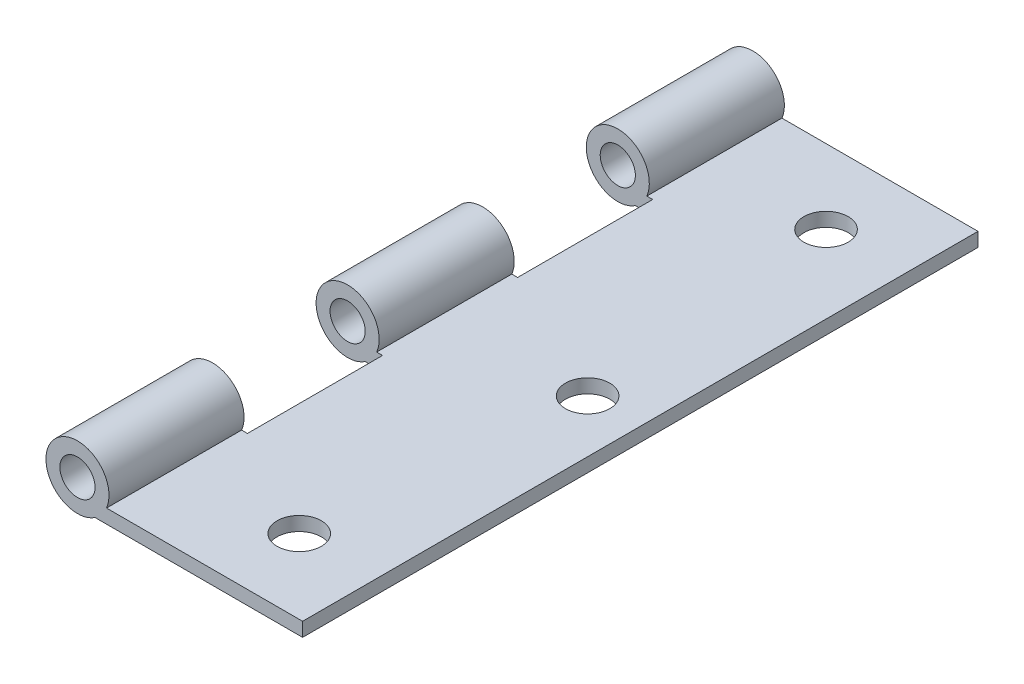
SolidWorks part; units mm, degrees
ref_plane "Front Plane" through (0, 0, 0) normal (0, 0, 1) x (1, 0, 0)
ref_plane "Top Plane" through (0, 0, 0) normal (0, 1, 0) x (1, 0, 0)
ref_plane "Right Plane" through (0, 0, 0) normal (1, 0, 0) x (0, 0, -1)
ref_plane "Plane1" through (0, 0, 38.1) normal (0, 0, 1) x (1, 0, 0)
sketch "Sketch1" plane through (0, 0, 38.1) normal (0, 0, 1) x (1, 0, 0)
  line L0 (25.4, -2.9508) -> (25.4, -1.376)
  line L1 (25.4, -1.376) -> (3.279, -1.376)
  line L2 (1.9844, -2.9508) -> (25.4, -2.9508)
  arc A0 (3.279, -1.376) -> (1.9844, -2.9508) centre (0, 0) ccw
extrude "Boss-Extrude1" add sketch "Sketch1" against normal blind 76.2
ref_plane "Plane2" through (0, 0, -22.86) normal (0, 0, -1) x (-1, 0, 0)
sketch "Sketch6" plane through (0, 0, -22.86) normal (0, 0, -1) x (-1, 0, 0)
  line L0 (-3.937, -1.376) -> (-3.937, -2.9508)
  line L1 (-3.937, -2.9508) -> (-1.9844, -2.9508)
  line L2 (-3.279, -1.376) -> (-3.937, -1.376)
  arc A0 (-1.9844, -2.9508) -> (-3.279, -1.376) centre (0, 0) ccw
extrude "Cut-Extrude1" cut sketch "Sketch6" against normal blind 15.24
ref_plane "Plane3" through (0, 0, 7.62) normal (0, 0, -1) x (-1, 0, 0)
sketch "Sketch12" plane through (0, 0, 7.62) normal (0, 0, -1) x (-1, 0, 0)
  line L0 (-3.937, -1.376) -> (-3.937, -2.9508)
  line L1 (-3.937, -2.9508) -> (-1.9844, -2.9508)
  line L2 (-3.279, -1.376) -> (-3.937, -1.376)
  arc A0 (-1.9844, -2.9508) -> (-3.279, -1.376) centre (0, 0) ccw
extrude "Cut-Extrude2" cut sketch "Sketch12" against normal blind 15.24
hole_wizard "CSK for M3 Flat Head Machine Screw1" positions "Sketch14" profile "Sketch13" countersink size "M3" standard "ANSI Metric"
sketch "Sketch14" plane through (0, -1.376, 0) normal (0, 1, 0) x (1, 0, 0)
  point P0 (16.637, 29.718)
  point P1 (16.637, -29.718)
  point P2 (19.4564, 0)
sketch "Sketch13" plane through (16.637, -1.376, -29.718) normal (1, 0, 0) x (0, 0, 1)
  line L0 (0, 0) -> (0, 2.18)
  line L1 (0, 2.18) -> (1.7526, 2.18)
  line L2 (1.7526, 2.18) -> (1.7526, 0.7874)
  line L3 (1.7526, 0.7874) -> (2.4371, 0)
  line L5 (2.4371, 0) -> (0, 0)
  line L6 (-1.7526, 0.7874) -> (-2.4371, 0) construction
  line L11 (0, -6.35) -> (0, 107.95) construction
  dimension "Thru Hole Dia." = 3.5052
  dimension "Thru Hole Depth" = 2.18
  dimension "Near C'Sink Dia." = 4.8742
  dimension "Near C'Sink Angle" = 82
hole_wizard "M3.5 Clearance Hole1" positions "Sketch16" profile "Sketch15" hole size "M3.5" standard "ANSI Metric"
sketch "Sketch16" plane through (0, 0, 38.1) normal (0, 0, 1) x (1, 0, 0)
  point P0 (0, 0)
sketch "Sketch15" plane through (0, 0, 38.1) normal (1, 0, 0) x (0, -1, 0)
  line L0 (0, 0) -> (0, 15.24)
  line L1 (0, 15.24) -> (1.9844, 15.24)
  line L2 (1.9844, 15.24) -> (1.9844, 0)
  line L5 (1.9844, 0) -> (0, 0)
  line L11 (0, -6.35) -> (0, 107.95) construction
  dimension "Thru Hole Dia." = 3.9688
  dimension "Thru Hole Depth" = 15.24
hole_wizard "M3.5 Clearance Hole2" positions "Sketch18" profile "Sketch17" hole size "M3.5" standard "ANSI Metric"
sketch "Sketch18" plane through (0, 0, -38.1) normal (0, 0, -1) x (-1, 0, 0)
  point P0 (0, 0)
sketch "Sketch17" plane through (0, 0, -38.1) normal (1, 0, 0) x (0, 1, 0)
  line L0 (0, 0) -> (0, 15.24)
  line L1 (0, 15.24) -> (1.9844, 15.24)
  line L2 (1.9844, 15.24) -> (1.9844, 0)
  line L5 (1.9844, 0) -> (0, 0)
  line L11 (0, -6.35) -> (0, 107.95) construction
  dimension "Thru Hole Dia." = 3.9688
  dimension "Thru Hole Depth" = 15.24
hole_wizard "M3.5 Clearance Hole3" positions "Sketch20" profile "Sketch19" hole size "M3.5" standard "ANSI Metric"
sketch "Sketch20" plane through (0, 0, -7.62) normal (0, 0, -1) x (-1, 0, 0)
  point P0 (0, 0)
sketch "Sketch19" plane through (0, 0, -7.62) normal (1, 0, 0) x (0, 1, 0)
  line L0 (0, 0) -> (0, 45.72)
  line L1 (0, 45.72) -> (1.9844, 45.72)
  line L2 (1.9844, 45.72) -> (1.9844, 0)
  line L5 (1.9844, 0) -> (0, 0)
  line L11 (0, -6.35) -> (0, 107.95) construction
  dimension "Thru Hole Dia." = 3.9688
  dimension "Thru Hole Depth" = 45.72
sketch "Sketch21" plane through (0, -1.376, 0) normal (0, 1, 0) x (1, 0, 0)
  circle A0 centre (16.637, 29.718) radius 2.5
  circle A1 centre (19.4564, 0) radius 2.5
  circle A2 centre (16.637, -29.718) radius 2.5
  dimension "D1" = 5
extrude "Cut-Extrude3" cut sketch "Sketch21" against normal up to surface (1.5748 mm away) up to face at (16.637, -2.9508, -31.4706)
